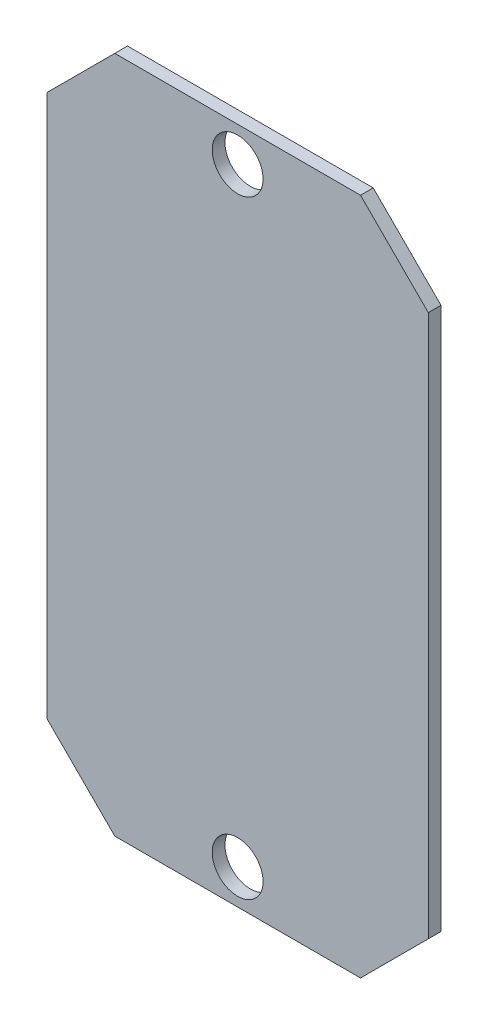
SolidWorks part; units mm, degrees
ref_plane "Plan de face" through (0, 0, 0) normal (0, 0, 1) x (1, 0, 0)
ref_plane "Plan de dessus" through (0, 0, 0) normal (0, 1, 0) x (1, 0, 0)
ref_plane "Plan de droite" through (0, 0, 0) normal (1, 0, 0) x (0, 0, -1)
sketch "Esquisse1" plane through (0, 0, 0) normal (0, 0, 1) x (1, 0, 0)
  line L1 (0, 0) -> (45, 0)
  line L2 (0, 0) -> (0, 80)
  line L3 (0, 80) -> (45, 80)
  line L4 (45, 0) -> (45, 80)
  dimension "D1" = 45
  dimension "D2" = 80
extrude "Boss.-Extru.1" add sketch "Esquisse1" along normal blind 1.5
chamfer "Chanfrein1" distance 8 angle 45 4 edges at (45, 80, 0.75) (45, 0, 0.75) (0, 0, 0.75) (0, 80, 0.75)
sketch "Esquisse2" plane through (0, 0, 1.5) normal (0, 0, 1) x (1, 0, 0)
  line L0 (22.5, 80) -> (22.5, 0) construction
  line L1 (37, 80) -> (8, 80) construction
  line L2 (8, 0) -> (37, 0) construction
  circle A0 centre (22.5, 75.9) radius 3
  circle A1 centre (22.5, 4.1) radius 3
  point P6 (22.5, 75.9)
  point P7 (22.5, 4.1)
  dimension "D1" = 4.1
  dimension "D2" = 4.1
extrude "Enlèv. mat.-Extru.1" cut sketch "Esquisse2" against normal through all
